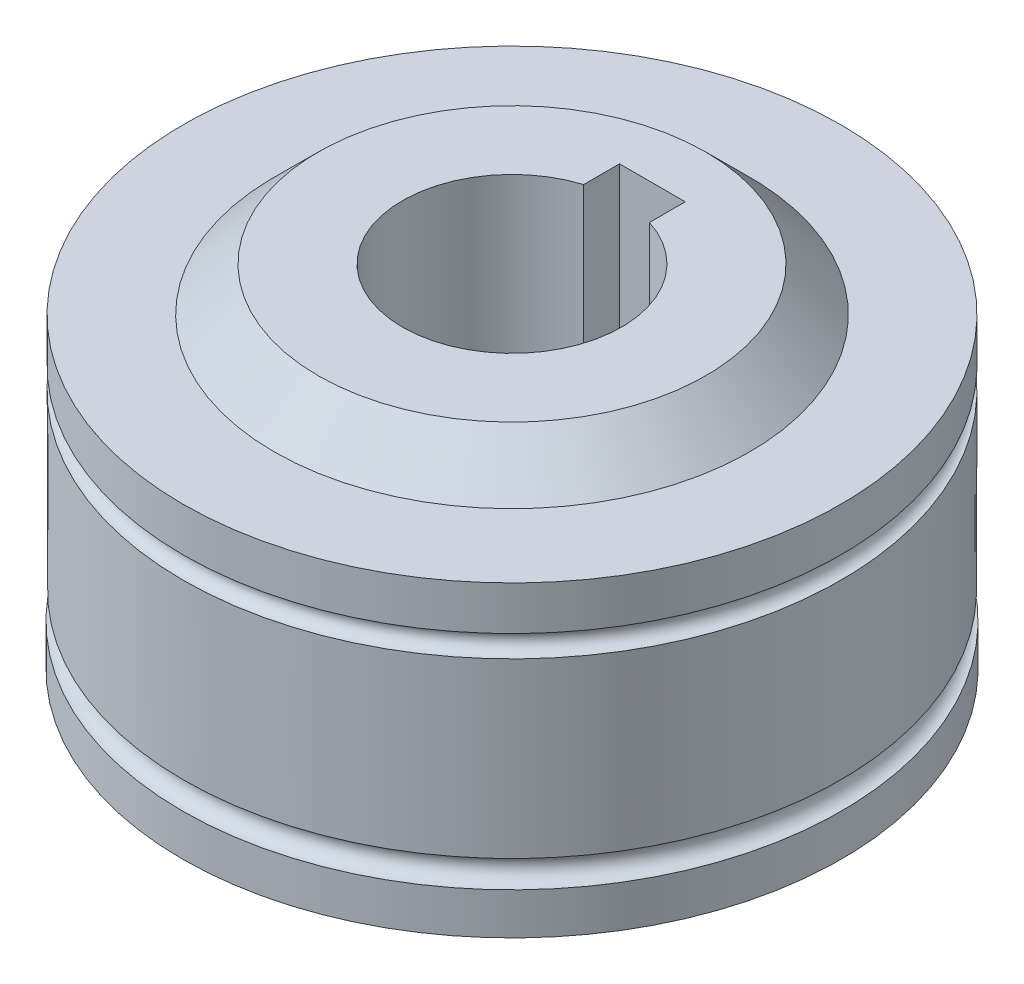
SolidWorks part; units mm, degrees
ref_plane "Спереди" through (0, 0, 0) normal (0, 0, 1) x (1, 0, 0)
ref_plane "Сверху" through (0, 0, 0) normal (0, 1, 0) x (1, 0, 0)
ref_plane "Справа" through (0, 0, 0) normal (1, 0, 0) x (0, 0, -1)
sketch "Эскиз1" plane through (0, 0, 0) normal (1, 0, 0) x (0, 0, -1)
  line L0 (0, 26.6332) -> (0, -20.8866) construction
  line L1 (15, 7) -> (15, 5)
  line L2 (10.8509, -7) -> (8.84, -9)
  line L3 (8.84, -9) -> (5, -9)
  line L4 (5, -9) -> (5, 9)
  line L5 (15.0346, -7) -> (15.0346, -5.0994)
  line L6 (15.0346, -7) -> (10.8509, -7)
  line L7 (15, 4) -> (14.9827, -3.9006)
  line L8 (15, 7) -> (10.8509, 7)
  line L9 (8.84, 9) -> (5, 9)
  line L10 (10.8509, 7) -> (8.84, 9)
  arc A0 (15, 5) -> (15, 4) centre (15, 4.5) ccw
  arc A1 (15.0346, -5.0994) -> (14.9827, -3.9006) centre (15.0087, -4.5) cw
revolve "Повернуть1" add sketch "Эскиз1" angle 360 about L0
sketch "Эскиз2" plane through (0, 9, 0) normal (0, 1, 0) x (1, 0, 0)
  line L0 (-1.5, 4) -> (-1.5, 6.4057)
  line L1 (-1.5, 6.4057) -> (1.5, 6.4057)
  line L2 (1.5, 6.4057) -> (1.5, 4)
  line L3 (-1.5, 4) -> (1.5, 4)
extrude "Вырез-Вытянуть1" cut sketch "Эскиз2" against normal through all
